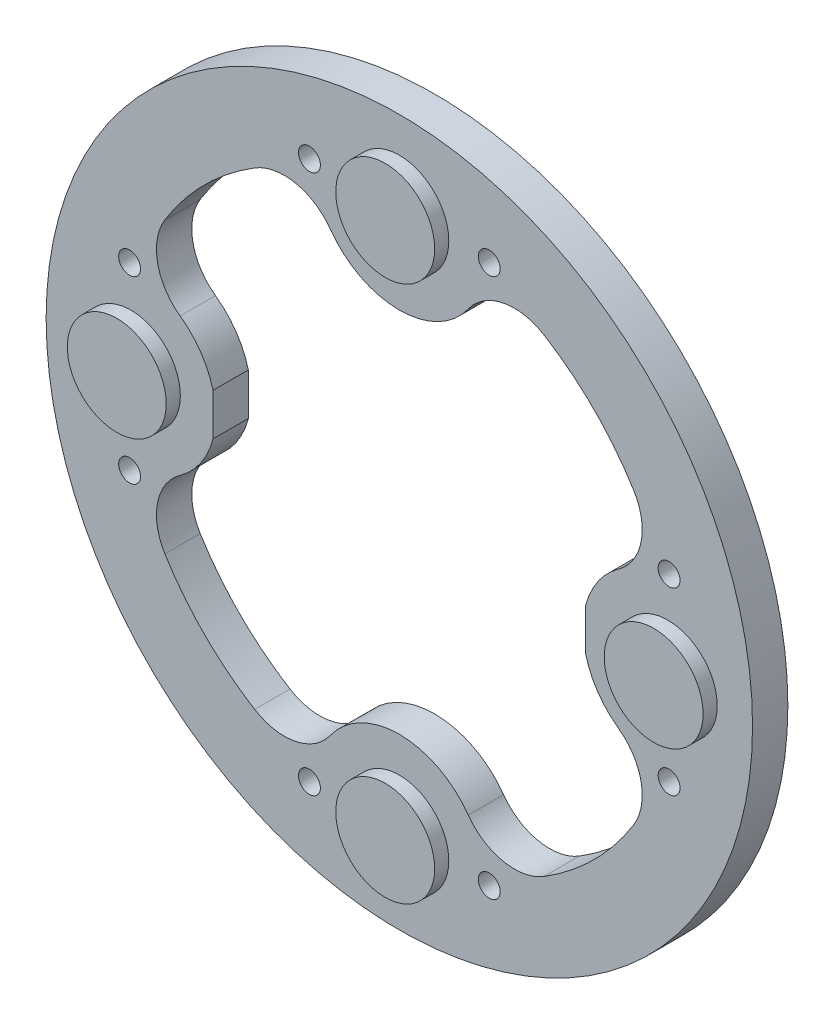
SolidWorks part; units mm, degrees
ref_plane "Front" through (0, 0, 0) normal (0, 0, 1) x (1, 0, 0)
ref_plane "Top" through (0, 0, 0) normal (0, 1, 0) x (1, 0, 0)
ref_plane "Right" through (0, 0, 0) normal (1, 0, 0) x (0, 0, -1)
sketch "Sketch1" plane through (0, 0, 0) normal (0, 0, 1) x (1, 0, 0)
  line L0 (-38, 0) -> (0, 0) construction
  line L1 (-26.375, -14) -> (-16.375, -14)
  line L2 (-26.375, -14) -> (-26.375, 14)
  line L3 (-26.375, 14) -> (-16.375, 14)
  line L4 (-16.375, -14) -> (-16.375, 14)
  line L5 (-26.375, -14) -> (-16.375, 14) construction
  line L6 (-26.375, 14) -> (-16.375, -14) construction
  line L7 (16.375, 14) -> (26.375, 14)
  line L8 (16.375, 14) -> (16.375, -14)
  line L9 (16.375, -14) -> (26.375, -14)
  line L10 (26.375, 14) -> (26.375, -14)
  line L11 (16.375, 14) -> (26.375, -14) construction
  line L12 (16.375, -14) -> (26.375, 14) construction
  line L13 (0, 38) -> (0, 0) construction
  line L14 (38, 0) -> (0, 0) construction
  line L15 (0, -38) -> (0, 0) construction
  circle A0 centre (0, 0) radius 50
  arc A1 (-33.1897, -20.4803) -> (-20.4803, -33.1897) centre (0, 0) ccw
  arc A2 (-31.0289, -9.7675) -> (-31.0289, 9.7675) centre (-38, 0) ccw
  circle A3 centre (0, 0) radius 39 construction
  arc A4 (-33.1897, -20.4803) -> (-31.0289, -9.7675) centre (-26.3816, -16.2792) cw
  arc A5 (-33.1897, 20.4803) -> (-31.0289, 9.7675) centre (-26.3816, 16.2792) ccw
  arc A6 (-20.4803, 33.1897) -> (-9.7675, 31.0289) centre (-16.2792, 26.3816) cw
  arc A7 (20.4803, 33.1897) -> (9.7675, 31.0289) centre (16.2792, 26.3816) ccw
  arc A8 (-9.7675, 31.0289) -> (9.7675, 31.0289) centre (0, 38) ccw
  arc A9 (33.1897, 20.4803) -> (31.0289, 9.7675) centre (26.3816, 16.2792) cw
  arc A10 (33.1897, -20.4803) -> (31.0289, -9.7675) centre (26.3816, -16.2792) ccw
  arc A11 (31.0289, 9.7675) -> (31.0289, -9.7675) centre (38, 0) ccw
  arc A12 (20.4803, -33.1897) -> (9.7675, -31.0289) centre (16.2792, -26.3816) cw
  arc A13 (-20.4803, -33.1897) -> (-9.7675, -31.0289) centre (-16.2792, -26.3816) ccw
  arc A14 (9.7675, -31.0289) -> (-9.7675, -31.0289) centre (0, -38) ccw
  arc A15 (20.4803, -33.1897) -> (33.1897, -20.4803) centre (0, 0) ccw
  arc A16 (33.1897, 20.4803) -> (20.4803, 33.1897) centre (0, 0) ccw
  arc A17 (-20.4803, 33.1897) -> (-33.1897, 20.4803) centre (0, 0) ccw
  point P3 (-21.375, 0)
  point P8 (21.375, 0)
  point P46 (0, 0)
  dimension "D1" = 100
  dimension "D9" = 38
  dimension "D10" = 12
  dimension "D11" = 8
  dimension "D2" = 28
  dimension "D3" = 10
  dimension "D4" = 28
  dimension "D5" = 10
  dimension "D6" = 32.75
  dimension "D7" = 16.375
  dimension "D8" = 11
  dimension "D12" = 4
extrude "Boss-Extrude1" add sketch "Sketch1" along normal blind 5 contours A0 A17 A6 A8 A7 A16 A9 A11 A10 A15 A12 A14 A13 A1 A4 A2 A5
sketch "Sketch2" plane through (0, 0, 5) normal (0, 0, 1) x (1, 0, 0)
  circle A0 centre (-38, 0) radius 7
  circle A1 centre (0, 38) radius 7
  circle A2 centre (38, 0) radius 7
  circle A3 centre (0, -38) radius 7
  point P12 (0, 0)
  dimension "D1" = 14
  dimension "D2" = 4
extrude "Boss-Extrude2" add sketch "Sketch2" along normal blind 2
sketch "Sketch3" plane through (0, 0, 5) normal (0, 0, 1) x (1, 0, 0)
  line L0 (0, 0) -> (-50, 0) construction
  line L1 (0, 0) -> (-35.3553, 35.3553) construction
  line L2 (-12.7279, 38.1838) -> (-25.4558, 25.4558) construction
  line L3 (-25.4558, 25.4558) -> (-38.1838, 12.7279) construction
  circle A0 centre (-12.7279, 38.1838) radius 1.55
  circle A1 centre (0, 0) radius 50 construction
  circle A2 centre (38.1838, 12.7279) radius 1.55
  circle A3 centre (12.7279, -38.1838) radius 1.55
  circle A4 centre (-38.1838, -12.7279) radius 1.55
  circle A5 centre (-38.1838, 12.7279) radius 1.55
  circle A6 centre (12.7279, 38.1838) radius 1.55
  circle A7 centre (38.1838, -12.7279) radius 1.55
  circle A8 centre (-12.7279, -38.1838) radius 1.55
  point P19 (0, 0)
  point P28 (0, 0)
  dimension "D1" = 3.1
  dimension "D7" = 3.1
  dimension "D2" = 45
  dimension "D3" = 36
  dimension "D4" = 18
  dimension "D6" = 18
  dimension "D5" = 4
  dimension "D8" = 4
extrude "Cut-Extrude1" cut sketch "Sketch3" against normal up to next
